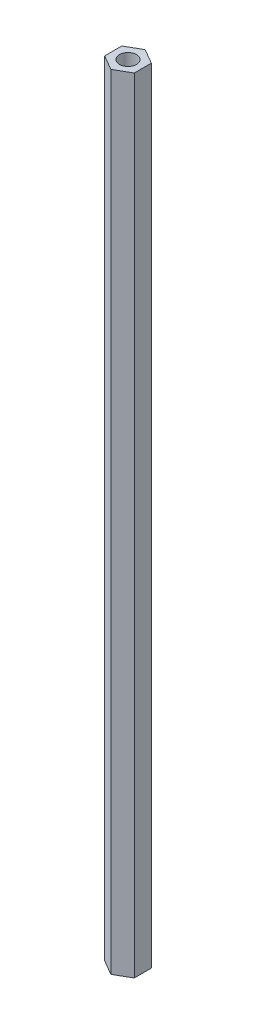
SolidWorks part; units mm, degrees
ref_plane "Face" through (0, 0, 0) normal (0, 0, 1) x (1, 0, 0)
ref_plane "Dessus" through (0, 0, 0) normal (0, 1, 0) x (1, 0, 0)
ref_plane "Droite" through (0, 0, 0) normal (1, 0, 0) x (0, 0, -1)
sketch "Esquisse1" plane through (0, 0, 0) normal (0, 1, 0) x (1, 0, 0)
  line L0 (0, 0) -> (0, 5.5688) construction
  line L1 (0, 5) -> (-4.3301, 2.5)
  line L2 (-4.3301, 2.5) -> (-4.3301, -2.5)
  line L3 (-4.3301, -2.5) -> (0, -5)
  line L4 (0, -5) -> (4.3301, -2.5)
  line L5 (4.3301, -2.5) -> (4.3301, 2.5)
  line L6 (4.3301, 2.5) -> (0, 5)
  circle A0 centre (0, 0) radius 4.3301 construction
  circle A1 centre (0, 0) radius 2.5
  dimension "D1" = 10
  dimension "D2" = 5
extrude "Extrusion1" add sketch "Esquisse1" along normal blind 229
